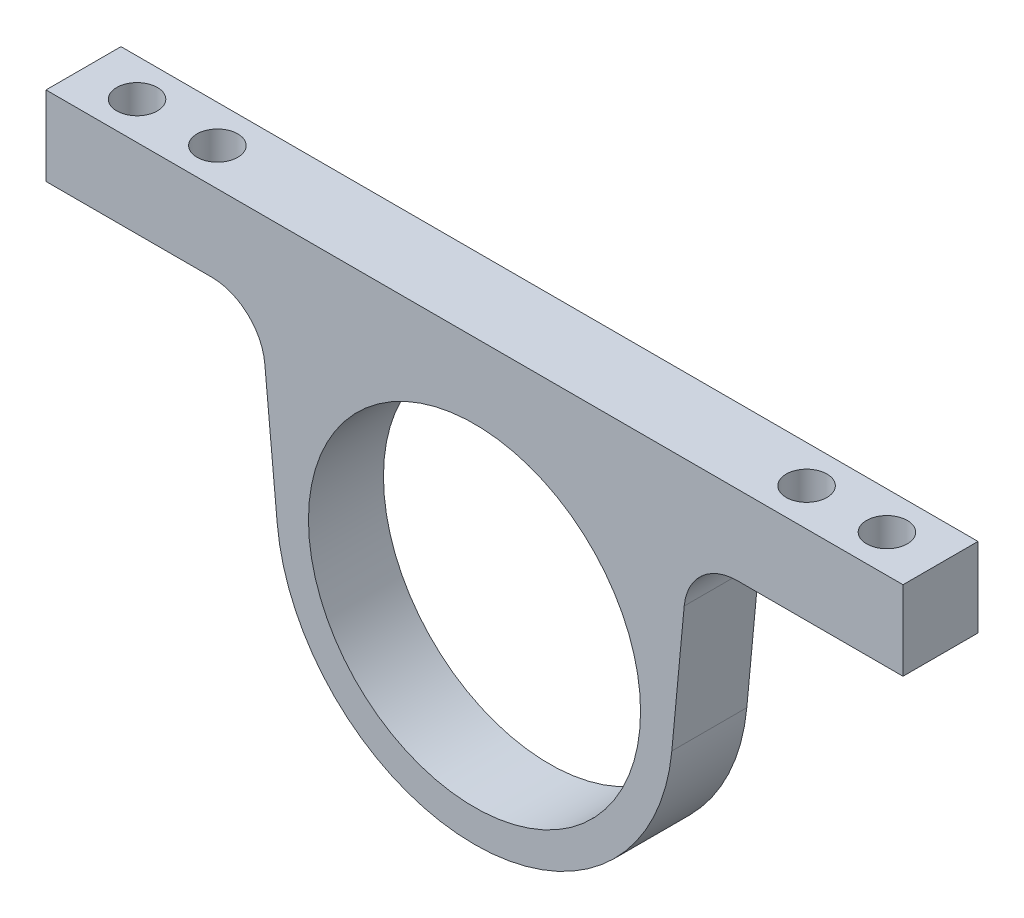
SolidWorks part; units mm, degrees
material "1.0037 (S235JR)"
ref_plane "Front Plane" through (0, 0, 0) normal (0, 0, 1) x (1, 0, 0)
ref_plane "Top Plane" through (0, 0, 0) normal (0, 1, 0) x (1, 0, 0)
ref_plane "Right Plane" through (0, 0, 0) normal (1, 0, 0) x (0, 0, -1)
sketch "Sketch1" plane through (0, 0, 0) normal (0, 0, 1) x (1, 0, 0)
  line L0 (-80, 45) -> (80, 45)
  line L1 (0, 0) -> (0, 45) construction
  line L2 (-80, 45) -> (-80, 30.1924)
  line L3 (-80, 30.1924) -> (-40, 30.1924)
  line L4 (-40, 30.1924) -> (-36.8377, -3.4614)
  line L5 (80, 45) -> (80, 30.1924)
  line L6 (80, 30.1924) -> (40, 30.1924)
  line L7 (40, 30.1924) -> (36.8377, -3.4614)
  circle A0 centre (0, 0) radius 31
  circle A1 centre (0, 0) radius 37
  dimension "D1" = 62
  dimension "D2" = 45
  dimension "D3" = 6
  dimension "D4" = 160
  dimension "D5" = 40
extrude "Boss-Extrude1" add sketch "Sketch1" along normal mid plane 14
fillet "Fillet1" radius 10 2 edges at (40, 30.1924, 0) (-40, 30.1924, 0)
sketch "Sketch3" plane through (0, 45, 0) normal (0, 1, 0) x (1, 0, 0)
  line L0 (-80, -7) -> (-80, 7) construction
  point P0 (-70, 0)
  point P3 (-55, 0)
  dimension "D1" = 10
  dimension "D2" = 15
hole_wizard "M7 Clearance Hole1" positions "3DSketch1" profile "Sketch4" hole size "M7" standard "ISO"
sketch3d "3DSketch1"
  point P0 (-70, 45, 0)
  point P3 (-55, 45, 0)
sketch "Sketch4" plane through (-70, 45, 0) normal (1, 0, 0) x (0, 0, 1)
  line L0 (0, 0) -> (0, 22.0333)
  line L1 (0, 22.0333) -> (3.8, 19.75)
  line L2 (3.8, 19.75) -> (3.8, 0)
  line L5 (3.8, 0) -> (0, 0)
  line L10 (0, 22.0333) -> (-3.8, 19.75) construction
  line L11 (0, -6.35) -> (0, 107.95) construction
  dimension "Hole Dia." = 7.6
  dimension "Hole Depth" = 19.75
  dimension "Drill Angle" = 118
mirror "Mirror1" about plane through (0, 0, 0) normal (1, 0, 0) of "M7 Clearance Hole1"
